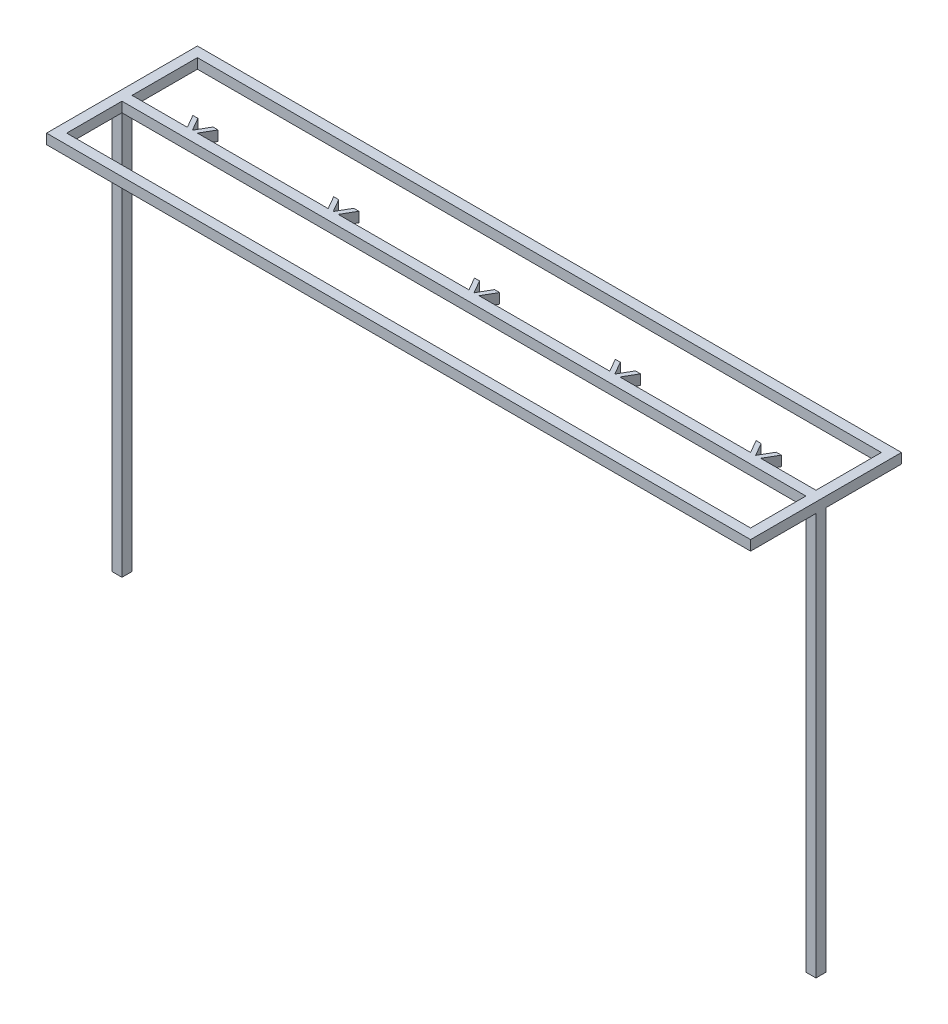
SolidWorks part; units mm, degrees
ref_plane "Front Plane" through (0, 0, 0) normal (0, 0, 1) x (1, 0, 0)
ref_plane "Top Plane" through (0, 0, 0) normal (0, 1, 0) x (1, 0, 0)
ref_plane "Right Plane" through (0, 0, 0) normal (1, 0, 0) x (0, 0, -1)
sketch "Sketch1" plane through (0, 0, 0) normal (0, 1, 0) x (1, 0, 0)
  line L1 (350, -75) -> (-350, -75)
  line L2 (350, -75) -> (350, 75)
  line L3 (350, 75) -> (-350, 75)
  line L4 (-350, -75) -> (-350, 75)
  line L5 (350, -75) -> (-350, 75) construction
  line L6 (350, 75) -> (-350, -75) construction
  point P0 (0, 0)
extrude "Boss-Extrude1" add sketch "Sketch1" along normal blind 10
sketch "Sketch2" plane through (0, 10, 0) normal (0, 1, 0) x (1, 0, 0)
  line L1 (340, -65) -> (-340, -65)
  line L2 (340, -65) -> (340, 65)
  line L3 (340, 65) -> (-340, 65)
  line L4 (-340, -65) -> (-340, 65)
  line L5 (340, -65) -> (-340, 65) construction
  line L6 (340, 65) -> (-340, -65) construction
  point P0 (0, 0)
extrude "Cut-Extrude1" cut sketch "Sketch2" against normal blind 10
sketch "Sketch3" plane through (0, 10, 0) normal (0, 1, 0) x (1, 0, 0)
  line L0 (-340, 65) -> (-340, -65) construction
  line L1 (340, 0) -> (-340, 0)
  line L2 (340, 0) -> (340, -10)
  line L3 (340, -10) -> (-340, -10)
  line L4 (-340, 0) -> (-340, -10)
  line L5 (340, 0) -> (-340, -10) construction
  line L6 (340, -10) -> (-340, 0) construction
  point P0 (0, -5)
extrude "Boss-Extrude2" add sketch "Sketch3" against normal blind 10
sketch "Sketch4" plane through (0, 0, 0) normal (0, 1, 0) x (1, 0, 0)
  line L0 (0, 0) -> (-7.5, 12.9904)
  line L1 (-7.5, 12.9904) -> (-12.5, 12.9904)
  line L2 (-12.5, 12.9904) -> (-5, 0)
  line L3 (340, 0) -> (-340, 0) construction
  line L4 (-5, 0) -> (0, 0)
  line L5 (0, 0) -> (7.5, 12.9904)
  line L6 (7.5, 12.9904) -> (12.5, 12.9904)
  line L7 (12.5, 12.9904) -> (5, 0)
  line L8 (5, 0) -> (0, 0)
  line L9 (147.5, 12.9904) -> (152.5, 12.9904)
  line L10 (140, 0) -> (147.5, 12.9904)
  line L11 (152.5, 12.9904) -> (145, 0)
  line L12 (145, 0) -> (140, 0)
  line L13 (140, 0) -> (132.5, 12.9904)
  line L14 (135, 0) -> (140, 0)
  line L15 (127.5, 12.9904) -> (135, 0)
  line L16 (132.5, 12.9904) -> (127.5, 12.9904)
  line L17 (287.5, 12.9904) -> (292.5, 12.9904)
  line L18 (280, 0) -> (287.5, 12.9904)
  line L19 (292.5, 12.9904) -> (285, 0)
  line L20 (285, 0) -> (280, 0)
  line L21 (280, 0) -> (272.5, 12.9904)
  line L22 (275, 0) -> (280, 0)
  line L23 (267.5, 12.9904) -> (275, 0)
  line L24 (272.5, 12.9904) -> (267.5, 12.9904)
  line L25 (-132.5, 12.9904) -> (-127.5, 12.9904)
  line L26 (-140, 0) -> (-132.5, 12.9904)
  line L27 (-127.5, 12.9904) -> (-135, 0)
  line L28 (-135, 0) -> (-140, 0)
  line L29 (-140, 0) -> (-147.5, 12.9904)
  line L30 (-145, 0) -> (-140, 0)
  line L31 (-152.5, 12.9904) -> (-145, 0)
  line L32 (-147.5, 12.9904) -> (-152.5, 12.9904)
  line L33 (-272.5, 12.9904) -> (-267.5, 12.9904)
  line L34 (-280, 0) -> (-272.5, 12.9904)
  line L35 (-267.5, 12.9904) -> (-275, 0)
  line L36 (-275, 0) -> (-280, 0)
  line L37 (-280, 0) -> (-287.5, 12.9904)
  line L38 (-285, 0) -> (-280, 0)
  line L39 (-292.5, 12.9904) -> (-285, 0)
  line L40 (-287.5, 12.9904) -> (-292.5, 12.9904)
  dimension "D1" = 3
  dimension "D2" = 3
extrude "Boss-Extrude3" add sketch "Sketch4" along normal blind 10 contours L8 L7 L6 L5 | L10 L9 L11 L12 | L13 L16 L15 L14 | L0 L1 L2 L4 | L26 L25 L27 L28 | L29 L32 L31 L30 | L34 L33 L35 L36 | L37 L40 L39 L38 | L21 L24 L23 L22 | L18 L17 L19 L20
sketch "Sketch5" plane through (0, 0, 0) normal (0, 1, 0) x (1, 0, 0)
  line L0 (-350, 75) -> (-350, -75) construction
  line L1 (-340, 0) -> (-350, 0)
  line L2 (-340, 0) -> (-340, -10)
  line L3 (-340, -10) -> (-350, -10)
  line L4 (-350, 0) -> (-350, -10)
  line L5 (350, -75) -> (350, 75) construction
  line L6 (340, 0) -> (350, 0)
  line L7 (340, 0) -> (340, -10)
  line L8 (340, -10) -> (350, -10)
  line L9 (350, 0) -> (350, -10)
extrude "Boss-Extrude4" add sketch "Sketch5" against normal blind 400
